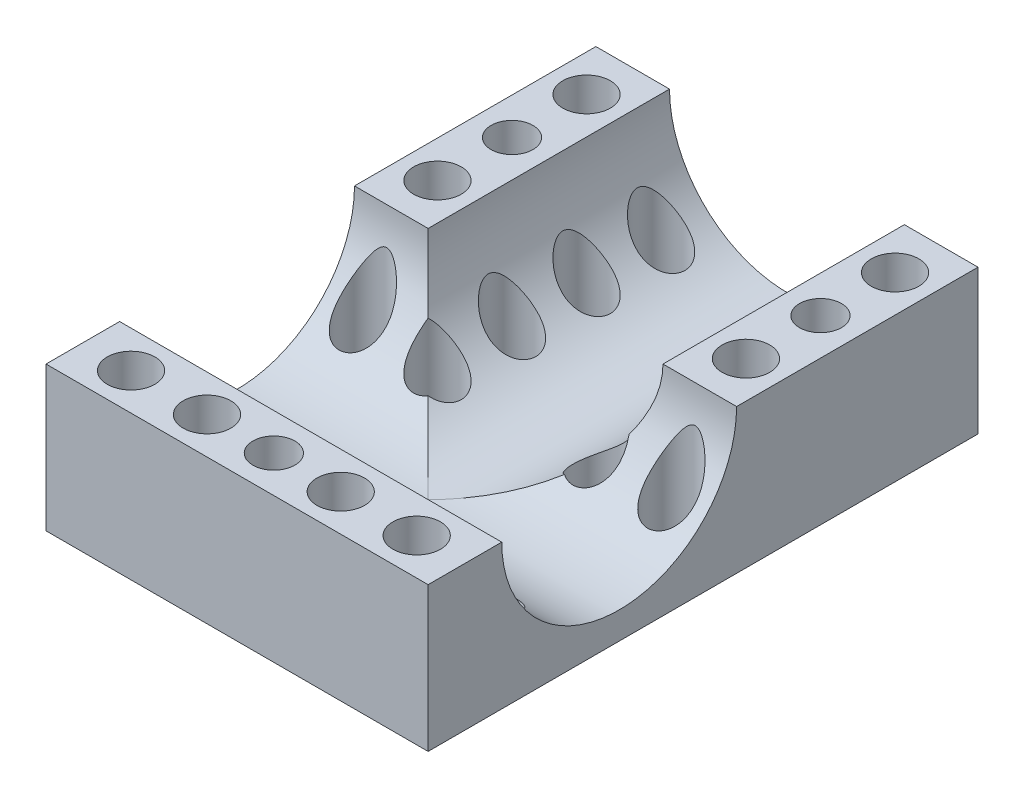
SolidWorks part; units mm, degrees
material "3.1355 (EN-AW 2024)"
ref_plane "Front" through (0, 0, 0) normal (0, 0, 1) x (1, 0, 0)
ref_plane "Top" through (0, 0, 0) normal (0, 1, 0) x (1, 0, 0)
ref_plane "Right" through (0, 0, 0) normal (1, 0, 0) x (0, 0, -1)
sketch "Эскиз1" plane through (0, 0, 0) normal (0, 1, 0) x (1, 0, 0)
  line L0 (0, 0) -> (8, 0)
  line L1 (8, 0) -> (33, 0)
  line L2 (33, 0) -> (41, 0)
  line L3 (0, 0) -> (0, 8)
  line L4 (0, 8) -> (0, 33)
  line L5 (0, 33) -> (0, 41)
  line L6 (0, 41) -> (0, 51)
  line L7 (0, 51) -> (0, 59)
  line L8 (0, 59) -> (41, 59)
  line L9 (41, 59) -> (41, 0)
  dimension "D1" = 8
  dimension "D2" = 25
  dimension "D3" = 8
  dimension "D4" = 8
  dimension "D5" = 25
  dimension "D6" = 8
  dimension "D7" = 10
  dimension "D8" = 8
extrude "Бобышка-Вытянуть1" add sketch "Эскиз1" along normal blind 15.5
sketch "Эскиз4" plane through (0, 0, 0) normal (-1, 0, 0) x (0, 0, 1)
  line L0 (-33, 0) -> (-8, 0) construction
  line L1 (-33, 0) -> (-41, 0) construction
  line L2 (-8, 0) -> (-33, 0) construction
  line L3 (-20.5, 0) -> (-20.5, 15.5) construction
  line L4 (-59, 15.5) -> (0, 15.5) construction
  line L5 (-33.1, 15.5) -> (-7.9, 15.5)
  arc A0 (-33.1, 15.5) -> (-7.9, 15.5) centre (-20.5, 15.5) ccw
  dimension "D1" = 12.6
extrude "Вырез-Вытянуть1" cut sketch "Эскиз4" against normal through all
sketch "Эскиз5" plane through (0, 0, -59) normal (0, 0, -1) x (-1, 0, 0)
  line L0 (-20.5, 15.5) -> (-20.5, 0) construction
  line L1 (-41, 15.5) -> (0, 15.5) construction
  line L2 (0, 0) -> (-41, 0) construction
  line L3 (-33.1, 15.5) -> (-7.9, 15.5)
  arc A0 (-33.1, 15.5) -> (-7.9, 15.5) centre (-20.5, 15.5) ccw
  dimension "D1" = 12.6
extrude "Вырез-Вытянуть2" cut sketch "Эскиз5" against normal blind 38.5
sketch "Эскиз7" plane through (0, 0, 0) normal (0, -1, 0) x (1, 0, 0)
  line L4 (41, 0) -> (0, 0)
  line L5 (0, 0) -> (0, -59)
  line L6 (0, -59) -> (41, -59)
  line L7 (41, -59) -> (41, 0)
  line L8 (41, 0) -> (0, 0)
  line L9 (0, 0) -> (0, -59)
  line L10 (0, -59) -> (41, -59)
  line L11 (41, -59) -> (41, 0)
  dimension "D1" = 0
ref_plane "Плоскость1" through (0, 2.9, 0) normal (0, 1, 0) x (1, 0, 0)
sketch "Эскиз6" plane through (0, 2.9, 0) normal (0, -1, 0) x (1, 0, 0)
  line L0 (20.5, -7.9) -> (20.5, -33.1) construction
  line L1 (41, -7.9) -> (0, -7.9) construction
  line L2 (0, -33.1) -> (41, -33.1) construction
  circle A0 centre (20.5, -20.5) radius 6 construction
  point P11 (20.5, -14.5)
  point P12 (26.5, -20.5)
  point P13 (20.5, -26.5)
  point P14 (14.5, -20.5)
  dimension "D1" = 12
extrude "Бобышка-Вытянуть2" [suppressed] add sketch "Эскиз7" along normal blind 4
sketch "Эскиз14" [suppressed] plane through (0, 2.9, 0) normal (0, 1, 0) x (1, 0, 0)
  circle A0 centre (20.5, 26.5) radius 4
  circle A1 centre (26.5, 20.5) radius 4
  circle A2 centre (20.5, 14.5) radius 4
  circle A3 centre (14.5, 20.5) radius 4
  point P12 (20.5, 20.5)
  dimension "D1" = 8
  dimension "D2" = 4
extrude "Вырез-Вытянуть3" [suppressed] cut sketch "Эскиз14" along normal through all
hole_wizard "Цековка для винта с внутренним шестигранником M44" [suppressed] positions "Эскиз19" profile "Эскиз15" counterbore size "M4" standard "Ansi Metric"
sketch "Эскиз19" [suppressed] plane through (0, 2.9, 0) normal (0, 1, 0) x (1, 0, 0)
  point P0 (14.5, 20.5)
  point P3 (20.5, 26.5)
  point P6 (26.5, 20.5)
  point P9 (20.5, 14.5)
sketch "Эскиз15" plane through (14.5, 2.9, -20.5) normal (1, 0, 0) x (0, 0, 1)
  line L0 (0, 0) -> (0, 6.9)
  line L1 (0, 6.9) -> (2.25, 6.9)
  line L3 (2.25, 6.9) -> (2.25, 4)
  line L4 (2.25, 4) -> (4, 4)
  line L5 (4, 4) -> (4, 0)
  line L7 (4, 0) -> (0, 0)
  line L11 (0, -6.35) -> (0, 107.95) construction
  dimension "Диаметр сквозного отверстия" = 4.5
  dimension "Глубина сквозного отверстия" = 6.9
  dimension "Диаметр цековки" = 8
  dimension "Глубина цековки" = 4
sketch "Эскиз20" plane through (0, 15.5, 0) normal (0, 1, 0) x (1, 0, 0)
  line L1 (3.95, 59) -> (3.95, 33.1) construction
  line L2 (7.9, 59) -> (0, 59) construction
  line L3 (0, 33.1) -> (41, 33.1) construction
  line L4 (20.5, 59) -> (20.5, 7.9) construction
  line L5 (33.1, 59) -> (7.9, 59) construction
  line L6 (0, 20.5) -> (41, 20.5) construction
  line L7 (0, 33.1) -> (0, 7.9) construction
  line L8 (41, 7.9) -> (41, 33.1) construction
  line L9 (0, 3.95) -> (41, 3.95) construction
  line L10 (0, 7.9) -> (0, 0) construction
  line L11 (41, 0) -> (41, 7.9) construction
  point P17 (3.95, 46.05)
  point P18 (37.05, 46.05)
  point P25 (20.5, 3.95)
  point P26 (-7.3564, 17.7008)
hole_wizard "Отверстие обработанное метчиком M4x0.71" positions "Эскиз22" profile "Эскиз21" tap size "M4x0.7" standard "Ansi Metric" end condition through all
sketch "Эскиз22" plane through (0, 15.5, 0) normal (0, 1, 0) x (1, 0, 0)
  point P0 (3.95, 46.05)
  point P3 (37.05, 46.05)
  point P6 (20.5, 3.95)
sketch "Эскиз21" plane through (3.95, 15.5, -46.05) normal (1, 0, 0) x (0, 0, 1)
  line L0 (0, 0) -> (0, 15.5)
  line L1 (0, 15.5) -> (1.65, 15.5)
  line L2 (1.65, 15.5) -> (1.65, 0)
  line L5 (1.65, 0) -> (0, 0)
  line L11 (0, -6.35) -> (0, 107.95) construction
  dimension "Диаметр проходного сверла" = 3.3
  dimension "Глубина проходного сверла" = 15.5
cosmetic thread "Отверстие резьбы1" parameters "D2"=4
cosmetic thread "Отверстие резьбы2" parameters "D2"=4
cosmetic thread "Отверстие резьбы3" parameters "D2"=4
sketch "Эскиз23" plane through (0, 15.5, 0) normal (0, 1, 0) x (1, 0, 0)
  line L0 (3.95, 59) -> (3.95, 46.05) construction
  line L1 (3.95, 46.05) -> (3.95, 33.1) construction
  line L2 (20.5, 59) -> (20.5, 7.9) construction
  line L3 (0, 3.95) -> (18.5, 3.95) construction
  line L4 (0, 3.95) -> (41, 3.95) construction
  line L5 (0, 7.9) -> (0, 0) construction
  line L6 (3.95, 33.1) -> (3.95, 30.05) construction
  line L7 (5.175, 3.95) -> (5.175, 11.95) construction
  line L8 (11.95, 59) -> (11.95, 30.05) construction
  line L9 (33.1, 59) -> (7.9, 59) construction
  circle A0 centre (5.175, 3.95) radius 3.175 construction
  circle A1 centre (13.325, 3.95) radius 3.175 construction
  circle A2 centre (27.675, 3.95) radius 3.175 construction
  circle A3 centre (35.825, 3.95) radius 3.175 construction
  point P6 (3.95, 54.05)
  point P7 (3.95, 38.05)
  point P12 (37.05, 38.05)
  point P13 (37.05, 54.05)
  point P21 (2, 3.95)
  point P26 (8.35, 3.95)
  point P27 (10.15, 3.95)
  point P28 (16.5, 3.95)
  point P33 (37.05, 33.1)
  point P34 (35.825, 11.95)
  point P37 (37.05, 30.05)
  point P42 (11.95, 54.05)
  point P43 (11.95, 46.05)
  point P44 (11.95, 38.05)
  point P45 (29.05, 30.05)
  point P46 (29.05, 38.05)
  point P47 (29.05, 46.05)
  point P48 (29.05, 54.05)
  point P49 (27.675, 11.95)
  point P50 (13.325, 11.95)
  point P51 (20.5, 11.95)
  dimension "D2" = 6.35
  dimension "D4" = 6.35
  dimension "D1" = 18.5
  dimension "D3" = 2
  dimension "D5" = 2
  dimension "D6" = 1.8
  dimension "D7" = 8
  dimension "D8" = 8
  dimension "D9" = 8
  dimension "D10" = 8
  dimension "D11" = 8
  dimension "D12" = 8
  dimension "D13" = 8
  dimension "D14" = 8
hole_wizard "Отверстие обработанное метчиком 1/4-201" positions "Эскиз25" profile "Эскиз24" tap size "1/4-20" standard "Ansi Inch" end condition through all
sketch "Эскиз25" plane through (0, 15.5, 0) normal (0, 1, 0) x (1, 0, 0)
  point P0 (3.95, 54.05)
  point P3 (37.05, 54.05)
  point P6 (37.05, 38.05)
  point P9 (3.95, 38.05)
  point P12 (5.175, 3.95)
  point P15 (13.325, 3.95)
  point P18 (27.675, 3.95)
  point P21 (35.825, 3.95)
sketch "Эскиз24" plane through (3.95, 15.5, -54.05) normal (1, 0, 0) x (0, 0, 1)
  line L0 (0, 0) -> (0, 15.5)
  line L1 (0, 15.5) -> (2.5527, 15.5)
  line L2 (2.5527, 15.5) -> (2.5527, 0)
  line L5 (2.5527, 0) -> (0, 0)
  line L11 (0, -6.35) -> (0, 107.95) construction
  dimension "Диаметр проходного сверла" = 5.1054
  dimension "Глубина проходного сверла" = 15.5
cosmetic thread "Отверстие резьбы4" parameters "D2"=6.35
cosmetic thread "Отверстие резьбы5" parameters "D2"=6.35
cosmetic thread "Отверстие резьбы6" parameters "D2"=6.35
cosmetic thread "Отверстие резьбы7" parameters "D2"=6.35
cosmetic thread "Отверстие резьбы8" parameters "D2"=6.35
cosmetic thread "Отверстие резьбы9" parameters "D2"=6.35
cosmetic thread "Отверстие резьбы10" parameters "D2"=6.35
cosmetic thread "Отверстие резьбы11" parameters "D2"=6.35
hole_wizard "Отверстие обработанное метчиком 1/4-202" positions "Эскиз28" profile "Эскиз27" tap size "1/4-20" standard "Ansi Inch" end condition through all
sketch "Эскиз28" plane through (0, 15.5, 0) normal (0, 1, 0) x (1, 0, 0)
  point P0 (3.95, 30.05)
  point P3 (37.05, 30.05)
  point P6 (35.825, 11.95)
  point P9 (5.175, 11.95)
sketch "Эскиз27" plane through (3.95, 15.5, -30.05) normal (1, 0, 0) x (0, 0, 1)
  line L0 (0, 0) -> (0, 15.5)
  line L1 (0, 15.5) -> (2.5527, 15.5)
  line L2 (2.5527, 15.5) -> (2.5527, 0)
  line L5 (2.5527, 0) -> (0, 0)
  line L11 (0, -6.35) -> (0, 107.95) construction
  dimension "Диаметр проходного сверла" = 5.1054
  dimension "Глубина проходного сверла" = 15.5
cosmetic thread "Отверстие резьбы12" parameters "D2"=6.35
cosmetic thread "Отверстие резьбы13" parameters "D2"=6.35
cosmetic thread "Отверстие резьбы14" parameters "D2"=6.35
cosmetic thread "Отверстие резьбы15" parameters "D2"=6.35
hole_wizard "Отверстие обработанное метчиком 1/4-203" positions "Эскиз30" profile "Эскиз29" tap size "1/4-20" standard "Ansi Inch" end condition through all
sketch "Эскиз30" plane through (0, 15.5, 0) normal (0, 1, 0) x (1, 0, 0)
  point P0 (11.95, 54.05)
  point P3 (11.95, 46.05)
  point P6 (11.95, 38.05)
  point P9 (11.95, 30.05)
  point P12 (29.05, 54.05)
  point P15 (29.05, 46.05)
  point P18 (29.05, 38.05)
  point P21 (29.05, 30.05)
sketch "Эскиз29" plane through (11.95, 15.5, -54.05) normal (1, 0, 0) x (0, 0, 1)
  line L0 (0, 0) -> (0, 15.5)
  line L1 (0, 15.5) -> (2.5527, 15.5)
  line L2 (2.5527, 15.5) -> (2.5527, 0)
  line L5 (2.5527, 0) -> (0, 0)
  line L11 (0, -6.35) -> (0, 107.95) construction
  dimension "Диаметр проходного сверла" = 5.1054
  dimension "Глубина проходного сверла" = 15.5
cosmetic thread "Отверстие резьбы16" parameters "D2"=6.35
cosmetic thread "Отверстие резьбы17" parameters "D2"=6.35
cosmetic thread "Отверстие резьбы18" parameters "D2"=6.35
cosmetic thread "Отверстие резьбы19" parameters "D2"=6.35
cosmetic thread "Отверстие резьбы20" parameters "D2"=6.35
cosmetic thread "Отверстие резьбы21" parameters "D2"=6.35
cosmetic thread "Отверстие резьбы22" parameters "D2"=6.35
cosmetic thread "Отверстие резьбы23" parameters "D2"=6.35
sketch "Эскиз31" plane through (0, 0, 0) normal (0, -1, 0) x (1, 0, 0)
  circle A0 centre (3.95, -46.05) radius 2.25
  circle A1 centre (37.05, -46.05) radius 2.25
  circle A2 centre (20.5, -3.95) radius 2.25
  dimension "D1" = 4.5
  dimension "D2" = 4.5
  dimension "D3" = 4.5
extrude "Вырез-Вытянуть4" cut sketch "Эскиз31" against normal through all
hole_wizard "Отверстие обработанное метчиком 1/4-204" positions "Эскиз33" profile "Эскиз32" tap size "1/4-20" standard "Ansi Inch" end condition through all
sketch "Эскиз33" plane through (0, 15.5, 0) normal (0, 1, 0) x (1, 0, 0)
  point P0 (27.675, 11.95)
  point P3 (13.325, 11.95)
  point P7 (20.5, 11.95)
sketch "Эскиз32" plane through (27.675, 15.5, -11.95) normal (1, 0, 0) x (0, 0, 1)
  line L0 (0, 0) -> (0, 15.5)
  line L1 (0, 15.5) -> (2.5527, 15.5)
  line L2 (2.5527, 15.5) -> (2.5527, 0)
  line L5 (2.5527, 0) -> (0, 0)
  line L11 (0, -6.35) -> (0, 107.95) construction
  dimension "Диаметр проходного сверла" = 5.1054
  dimension "Глубина проходного сверла" = 15.5
cosmetic thread "Отверстие резьбы24" parameters "D2"=6.35
cosmetic thread "Отверстие резьбы25" parameters "D2"=6.35
cosmetic thread "Отверстие резьбы26" parameters "D2"=6.35
equation "\"D1@Вырез-Вытянуть2\"=25.9+12.6"
equation "\"D4@Эскиз23\"=\"D2@Эскиз23\""
equation "\"D5@Эскиз23\"=\"D3@Эскиз23\""
equation "\"D2@Эскиз31\"=\"D1@Эскиз31\""
equation "\"D3@Эскиз31\"=\"D1@Эскиз31\""
